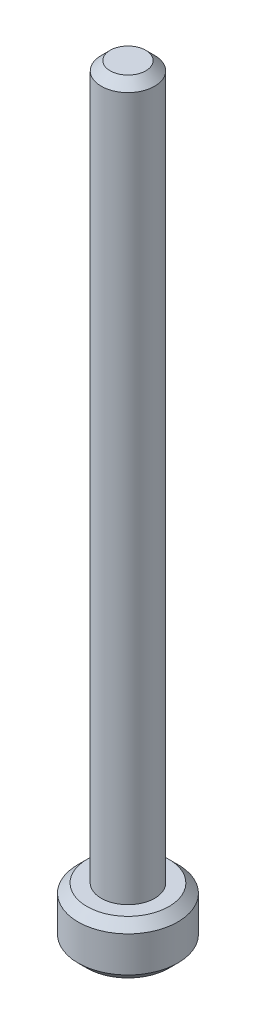
SolidWorks part; units mm, degrees
material "Zinc AC43A (Zn-4Al-2.5Cu-0.04Mg; Number 2 Die Casting Alloy; Zamak 2), Die Cast"
ref_plane "Plano frontal" through (0, 0, 0) normal (0, 0, 1) x (1, 0, 0)
ref_plane "Plano superior" through (0, 0, 0) normal (0, 1, 0) x (1, 0, 0)
ref_plane "Plano direito" through (0, 0, 0) normal (1, 0, 0) x (0, 0, -1)
sketch "Sketch1" plane through (0, 0, 0) normal (0, 1, 0) x (1, 0, 0)
  circle A0 centre (0, 0) radius 2.8
  dimension "D1" = 5.6
extrude "Boss-Extrude1" add sketch "Sketch1" along normal mid plane 3
sketch "Sketch2" plane through (0, 1.5, 0) normal (0, 1, 0) x (1, 0, 0)
  circle A0 centre (0, 0) radius 1.5
  dimension "D1" = 3
extrude "Boss-Extrude2" add sketch "Sketch2" along normal blind 40
chamfer "Chamfer1" distance 0.5 angle 45 1 edges at (0, 41.5, 1.5)
chamfer "Chamfer2" distance 0.5 angle 45 2 edges at (0, 1.5, 2.8) (0, -1.5, 2.8)
